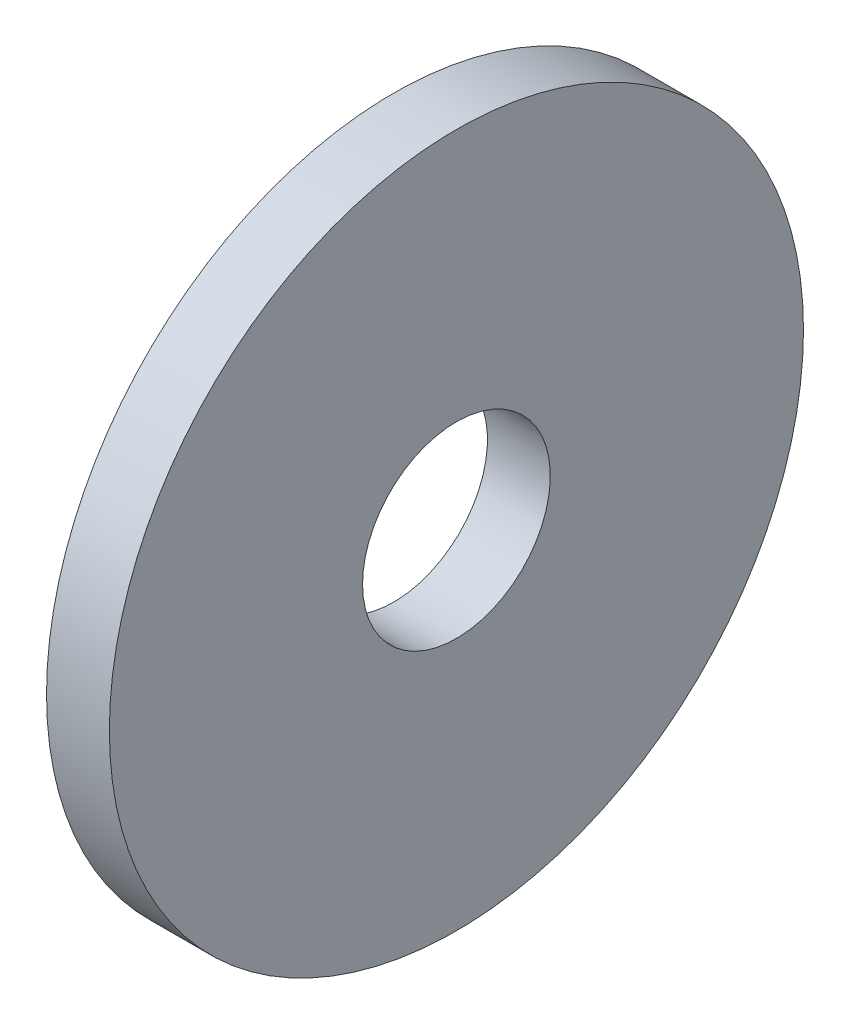
SolidWorks part; units mm, degrees
ref_plane "Plane1" through (0, 0, 0) normal (0, 0, 1) x (1, 0, 0)
ref_plane "Plane2" through (0, 0, 0) normal (0, 1, 0) x (1, 0, 0)
ref_plane "Plane3" through (0, 0, 0) normal (1, 0, 0) x (0, 0, -1)
sketch "Sketch1" plane through (0, 0, 0) normal (0, 0, 1) x (1, 0, 0)
  line L0 (-34.925, 0) -> (9.525, 0) construction
  line L1 (0, 3.435) -> (0, 12.7)
  line L2 (0, 12.7) -> (-2.3, 12.7)
  line L3 (-2.3, 12.7) -> (-2.3, 3.435)
  line L4 (-2.3, 3.435) -> (0, 3.435)
  dimension "Thickness" = 2.3
  dimension "Inside_dia" = 6.87
  dimension "Outside_dia" = 25.4
revolve "Base-Revolve" add sketch "Sketch1" angle 360 about L0
